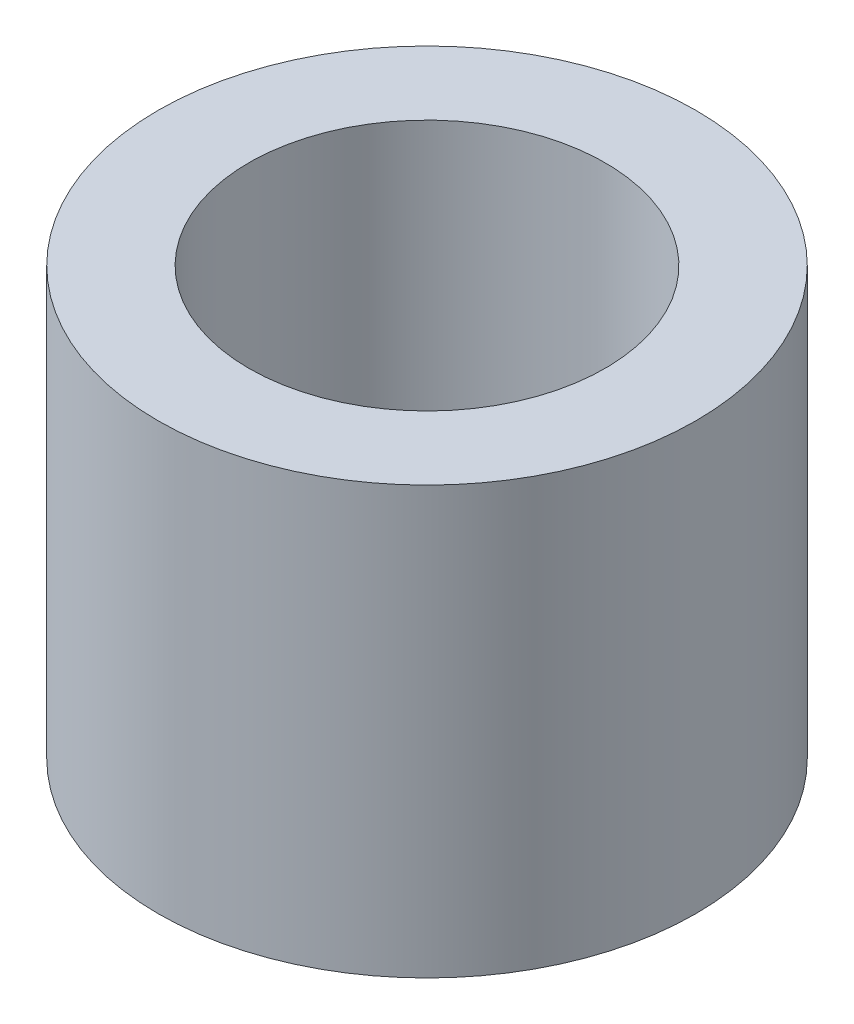
SolidWorks part; units mm, degrees
ref_plane "Front Plane" through (0, 0, 0) normal (0, 0, 1) x (1, 0, 0)
ref_plane "Top Plane" through (0, 0, 0) normal (0, 1, 0) x (1, 0, 0)
ref_plane "Right Plane" through (0, 0, 0) normal (1, 0, 0) x (0, 0, -1)
sketch "Sketch1" plane through (0, 0, 0) normal (0, 1, 0) x (1, 0, 0)
  circle A0 centre (0, 0) radius 4
  circle A1 centre (0, 0) radius 2.65
  dimension "D1" = 8
  dimension "D2" = 5.3
extrude "Boss-Extrude1" add sketch "Sketch1" along normal blind 6.35
